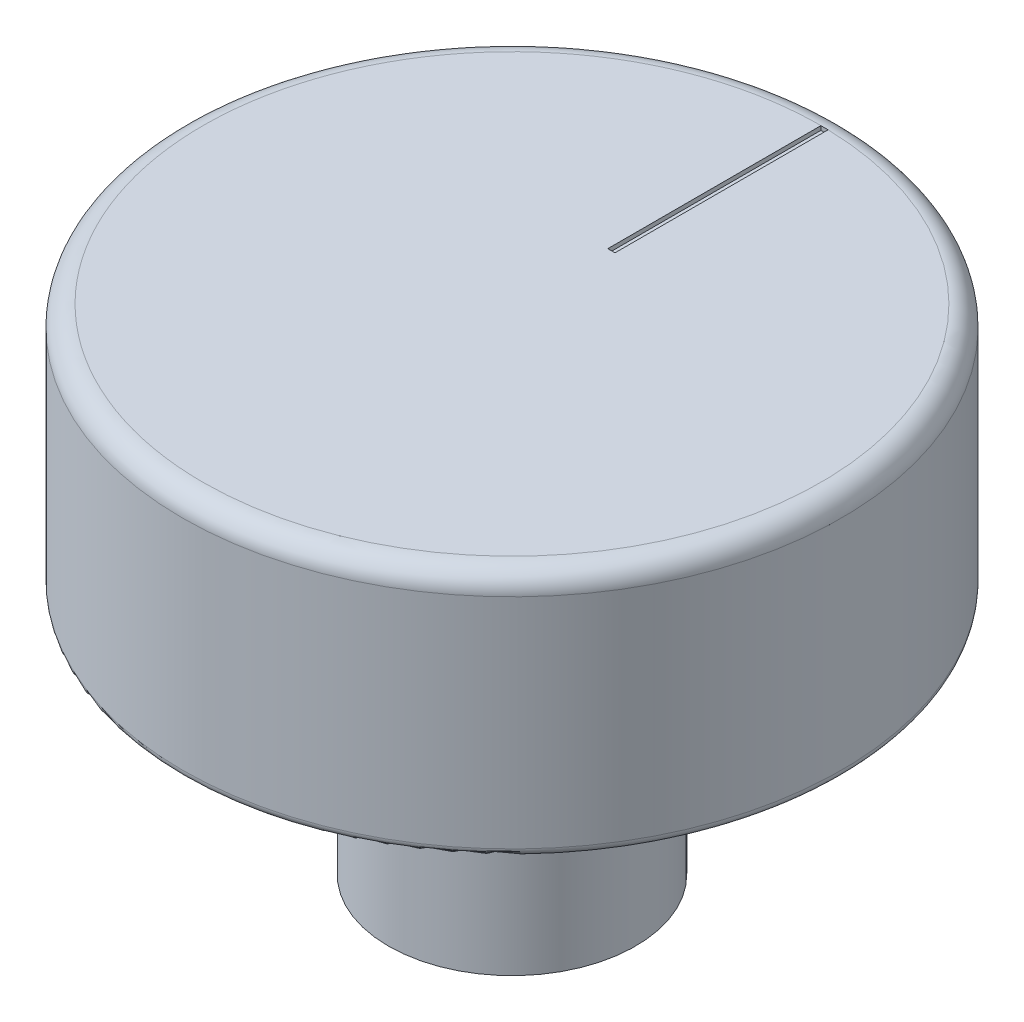
SolidWorks part; units mm, degrees
ref_plane "Front Plane" through (0, 0, 0) normal (0, 0, 1) x (1, 0, 0)
ref_plane "Top Plane" through (0, 0, 0) normal (0, 1, 0) x (1, 0, 0)
ref_plane "Right Plane" through (0, 0, 0) normal (1, 0, 0) x (0, 0, -1)
sketch "Sketch1" plane through (0, 0, 0) normal (0, 1, 0) x (1, 0, 0)
  circle A0 centre (0, 0) radius 3
extrude "Boss-Extrude1" add sketch "Sketch1" along normal blind 6
sketch "Sketch2" plane through (0, 6, 0) normal (0, 1, 0) x (1, 0, 0)
  circle A0 centre (0, 0) radius 8
extrude "Boss-Extrude2" add sketch "Sketch2" along normal blind 6 contours A0
fillet "Fillet2" radius 0.2 1 edges at (0, 6, 8)
fillet "Fillet3" radius 0.5 1 edges at (0, 12, 8)
sketch "Sketch5" plane through (0, 12, 0) normal (0, 1, 0) x (1, 0, 0)
  line L1 (0, 2.3255) -> (0.1752, 2.3255)
  line L2 (0, 2.3255) -> (0, 7.498)
  line L3 (0, 7.498) -> (0.1752, 7.498)
  line L4 (0.1752, 2.3255) -> (0.1752, 7.498)
  circle A0 centre (0, 0) radius 7.5 construction
extrude "Cut-Extrude1" cut sketch "Sketch5" against normal blind 0.1
